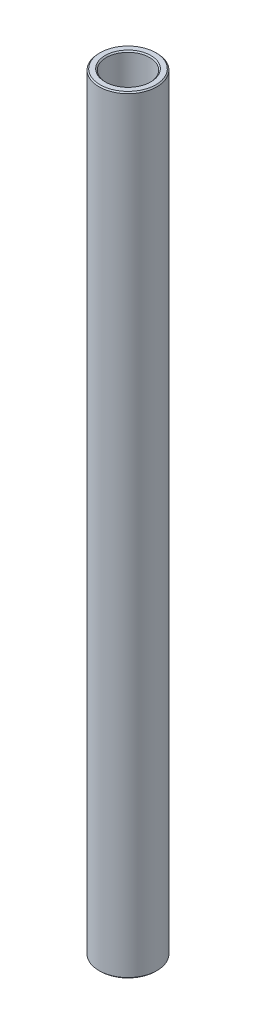
SolidWorks part; units mm, degrees
ref_plane "Front Plane" through (0, 0, 0) normal (0, 0, 1) x (1, 0, 0)
ref_plane "Top Plane" through (0, 0, 0) normal (0, 1, 0) x (1, 0, 0)
ref_plane "Right Plane" through (0, 0, 0) normal (1, 0, 0) x (0, 0, -1)
sketch "Sketch1" plane through (0, 0, 0) normal (0, 0, 1) x (1, 0, 0)
  line L0 (0, 11.6086) -> (0, -11.6086) construction
  line L1 (4.7625, 84.1375) -> (6.35, 84.1375)
  line L2 (6.35, 84.1375) -> (6.35, -84.1375)
  line L3 (6.35, -84.1375) -> (4.7625, -84.1375)
  line L4 (4.7625, -84.1375) -> (4.7625, 84.1375)
  line L5 (4.7625, 0) -> (0, 0) construction
  dimension "D1" = 9.525
  dimension "D2" = 12.7
  dimension "D3" = 168.275
revolve "Revolve1" add sketch "Sketch1" angle 360 about L0
chamfer "Chamfer1" distance 0.254 angle 45 4 edges at (-4.7625, -84.1375, 0) (-6.35, -84.1375, 0) (-6.35, 84.1375, 0) (-4.7625, 84.1375, 0)
